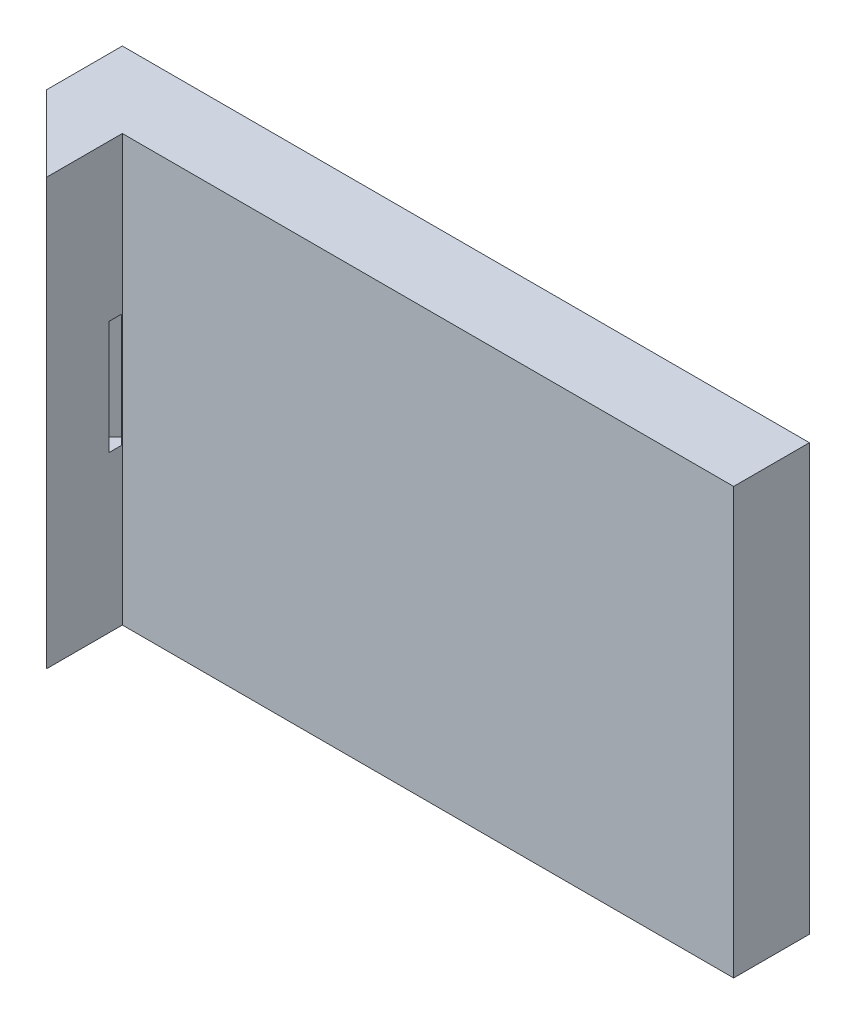
SolidWorks part; units mm, degrees
ref_plane "Front Plane" through (0, 0, 0) normal (0, 0, 1) x (1, 0, 0)
ref_plane "Top Plane" through (0, 0, 0) normal (0, 1, 0) x (1, 0, 0)
ref_plane "Right Plane" through (0, 0, 0) normal (1, 0, 0) x (0, 0, -1)
sketch "Sketch1" plane through (0, 0, 0) normal (0, 0, 1) x (1, 0, 0)
  line L1 (-175, -28.1) -> (175, -28.1)
  line L2 (-175, -28.1) -> (-175, 28.1)
  line L3 (-175, 28.1) -> (175, 28.1)
  line L4 (175, -28.1) -> (175, 28.1)
  line L5 (-175, -28.1) -> (175, 28.1) construction
  line L6 (-175, 28.1) -> (175, -28.1) construction
  point P0 (0, 0)
extrude "Boss-Extrude1" add sketch "Sketch1" along normal blind 10
sketch "Sketch2" plane through (0, 0, 10) normal (0, 0, 1) x (1, 0, 0)
  line L2 (175, 28.1) -> (-175, 28.1) construction
  line L3 (-28.1, -28.1) -> (28.1, -28.1)
  line L4 (-28.1, -28.1) -> (-28.1, 28.1)
  line L5 (-28.1, 28.1) -> (28.1, 28.1)
  line L6 (28.1, -28.1) -> (28.1, 28.1)
  point P8 (0, 0)
extrude "Cut-Extrude1" cut sketch "Sketch2" against normal blind 5
sketch "Sketch3" plane through (175, 0, 0) normal (1, 0, 0) x (0, 0, -1)
  line L1 (-10, 28.1) -> (0, 28.1)
  line L2 (-10, 28.1) -> (-10, -28.1)
  line L3 (-10, -28.1) -> (0, -28.1)
  line L4 (0, 28.1) -> (0, -28.1)
extrude "Boss-Extrude2" add sketch "Sketch3" along normal blind 10
sketch "Sketch4" plane through (0, 0, 10) normal (0, 0, 1) x (1, 0, 0)
  line L0 (28.1, -28.1) -> (185, -28.1) construction
  line L1 (185, 28.1) -> (175, 28.1)
  line L2 (185, 28.1) -> (185, -28.1)
  line L3 (185, -28.1) -> (175, -28.1)
  line L4 (175, 28.1) -> (175, -28.1)
extrude "Boss-Extrude3" add sketch "Sketch4" along normal blind 10
sketch "Sketch5" plane through (0, 28.1, 0) normal (0, 1, 0) x (1, 0, 0)
  line L0 (175, -20) -> (185, -10)
  line L1 (185, 0) -> (185, -20) construction
  line L2 (185, -10) -> (185, -20)
  line L3 (185, -20) -> (175, -20)
extrude "Cut-Extrude2" cut sketch "Sketch5" against normal blind 56.2
sketch "Sketch6" plane through (-175, 0, 0) normal (-1, 0, 0) x (0, 0, 1)
  line L1 (0, -28.1) -> (10, -28.1)
  line L2 (0, -28.1) -> (0, 28.1)
  line L3 (0, 28.1) -> (10, 28.1)
  line L4 (10, -28.1) -> (10, 28.1)
extrude "Boss-Extrude4" add sketch "Sketch6" along normal blind 10
sketch "Sketch7" plane through (0, 0, 10) normal (0, 0, 1) x (1, 0, 0)
  line L0 (-28.1, 28.1) -> (-185, 28.1) construction
  line L1 (-185, -28.1) -> (-175, -28.1)
  line L2 (-185, -28.1) -> (-185, 28.1)
  line L3 (-185, 28.1) -> (-175, 28.1)
  line L4 (-175, -28.1) -> (-175, 28.1)
extrude "Boss-Extrude5" add sketch "Sketch7" along normal blind 10
sketch "Sketch8" plane through (0, 28.1, 0) normal (0, 1, 0) x (1, 0, 0)
  line L0 (-175, -20) -> (-185, -10)
  line L1 (-185, -20) -> (-185, 0) construction
  line L2 (-185, -10) -> (-185, -20)
  line L3 (-185, -20) -> (-175, -20)
extrude "Cut-Extrude3" cut sketch "Sketch8" against normal blind 56.2
sketch "Sketch9" plane through (0, 0, 5) normal (0, 0, 1) x (1, 0, 0)
  line L3 (-15, -15) -> (15, -15)
  line L4 (-15, -15) -> (-15, 15)
  line L5 (-15, 15) -> (15, 15)
  line L6 (15, -15) -> (15, 15)
  point P4 (0, 0)
extrude "Cut-Extrude4" cut sketch "Sketch9" against normal blind 5
sketch "Sketch10" plane through (0, 0, 5) normal (0, 0, 1) x (1, 0, 0)
  circle A2 centre (21.55, 21.55) radius 3
  circle A3 centre (-21.55, -21.55) radius 3
  circle A4 centre (-21.55, 21.55) radius 3
  circle A5 centre (21.55, -21.55) radius 3
extrude "Cut-Extrude5" cut sketch "Sketch10" against normal blind 5
sketch "Sketch11" plane through (97.5, 0, 97.5) normal (0.7071, 0, 0.7071) x (0.7071, 0, -0.7071)
  line L3 (117.9226, -7.5) -> (115.4226, -7.5)
  line L4 (117.9226, -7.5) -> (117.9226, 7.5)
  line L5 (117.9226, 7.5) -> (115.4226, 7.5)
  line L6 (115.4226, -7.5) -> (115.4226, 7.5)
  line L7 (117.9226, -7.5) -> (115.4226, 7.5) construction
  line L8 (117.9226, 7.5) -> (115.4226, -7.5) construction
  point P6 (116.6726, 0)
extrude "Cut-Extrude6" cut sketch "Sketch11" against normal blind 7
sketch "Sketch12" plane through (-97.5, 0, 97.5) normal (-0.7071, 0, 0.7071) x (0.7071, 0, 0.7071)
  line L2 (-117.9226, 7.5) -> (-115.4226, 7.5)
  line L3 (-117.9226, 7.5) -> (-117.9226, -7.5)
  line L4 (-117.9226, -7.5) -> (-115.4226, -7.5)
  line L5 (-115.4226, 7.5) -> (-115.4226, -7.5)
  line L6 (-117.9226, 7.5) -> (-115.4226, -7.5) construction
  line L7 (-117.9226, -7.5) -> (-115.4226, 7.5) construction
  point P4 (-116.6726, 0)
extrude "Cut-Extrude7" cut sketch "Sketch12" against normal blind 7
sketch "Sketch14" plane through (0, 0, 10) normal (0, 0, 1) x (1, 0, 0)
  line L0 (-175, -28.1) -> (-28.1, -28.1) construction
  line L6 (-94.3, 28.1) -> (185, 28.1)
  line L7 (-94.3, 28.1) -> (-94.3, -28.1)
  line L8 (-94.3, -28.1) -> (185, -28.1)
  line L9 (185, 28.1) -> (185, -28.1)
extrude "Cut-Extrude10" cut sketch "Sketch14" against normal blind 10
